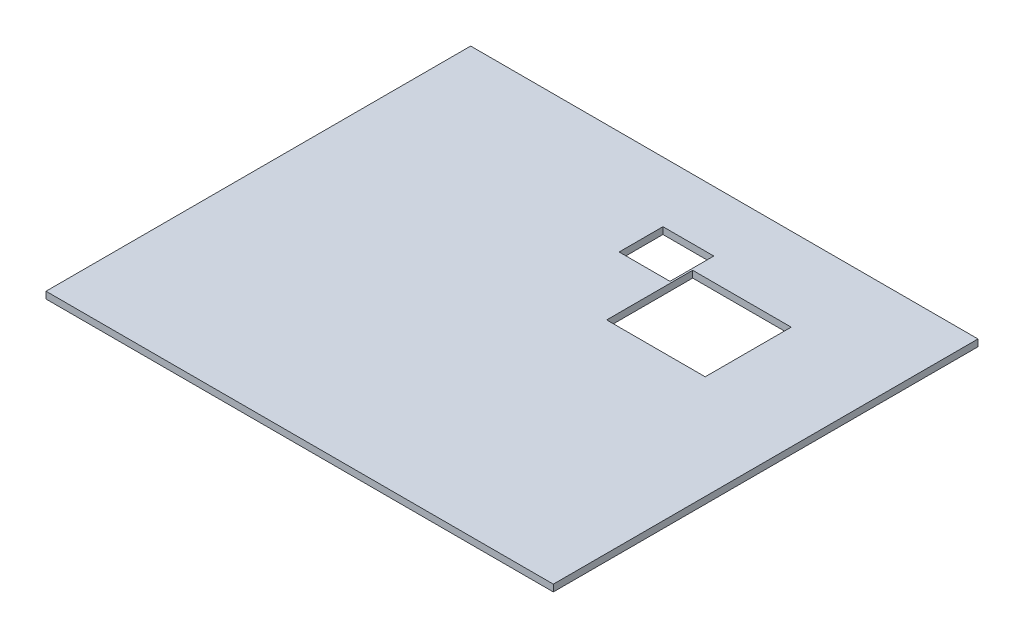
SolidWorks part; units mm, degrees
ref_plane "Front Plane" through (0, 0, 0) normal (0, 0, 1) x (1, 0, 0)
ref_plane "Top Plane" through (0, 0, 0) normal (0, 1, 0) x (1, 0, 0)
ref_plane "Right Plane" through (0, 0, 0) normal (1, 0, 0) x (0, 0, -1)
sketch "Sketch1" plane through (0, 0, 0) normal (0, 1, 0) x (1, 0, 0)
  line L1 (44.8, -37.5) -> (-44.8, -37.5)
  line L2 (44.8, -37.5) -> (44.8, 37.5)
  line L3 (44.8, 37.5) -> (-44.8, 37.5)
  line L4 (-44.8, -37.5) -> (-44.8, 37.5)
  line L5 (44.8, -37.5) -> (-44.8, 37.5) construction
  line L6 (44.8, 37.5) -> (-44.8, -37.5) construction
  line L7 (9.1, 7.62) -> (26.5, 7.62)
  line L8 (9.1, 7.62) -> (9.1, 22.81)
  line L9 (9.1, 22.81) -> (26.5, 22.81)
  line L10 (26.5, 7.62) -> (26.5, 22.81)
  line L11 (-0.19, 19.11) -> (8.79, 19.11)
  line L12 (-0.19, 19.11) -> (-0.19, 26.85)
  line L13 (-0.19, 26.85) -> (8.79, 26.85)
  line L14 (8.79, 19.11) -> (8.79, 26.85)
  point P0 (0, 0)
  dimension "D1" = 89.6
  dimension "D2" = 75
  dimension "D3" = 18.3
  dimension "D4" = 14.69
  dimension "D5" = 53.9
  dimension "D6" = 45.12
  dimension "D7" = 36.01
  dimension "D8" = 44.61
  dimension "D9" = 10.65
  dimension "D10" = 56.61
extrude "Boss-Extrude1" add sketch "Sketch1" along normal blind 1.2
